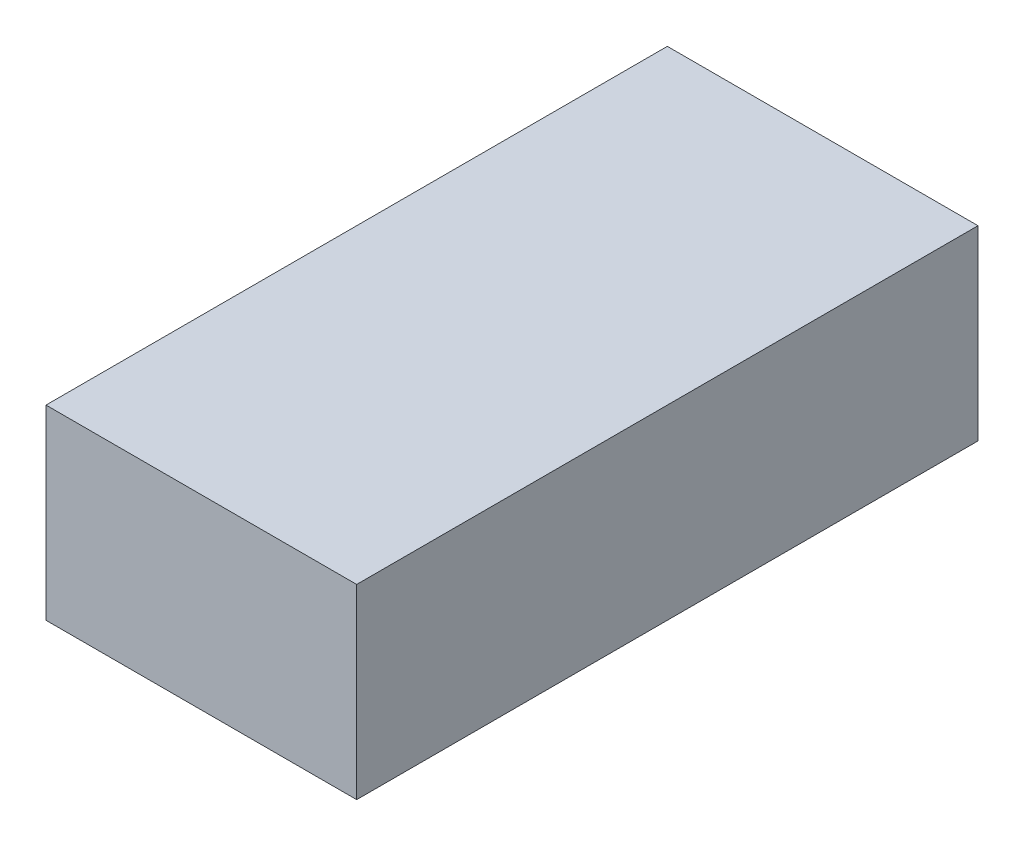
SolidWorks part; units mm, degrees
ref_plane "Front Plane" through (0, 0, 0) normal (0, 0, 1) x (1, 0, 0)
ref_plane "Top Plane" through (0, 0, 0) normal (0, 1, 0) x (1, 0, 0)
ref_plane "Right Plane" through (0, 0, 0) normal (1, 0, 0) x (0, 0, -1)
sketch "Sketch2" plane through (0, 0, 0) normal (1, 0, 0) x (0, 0, -1)
  line L3 (-262.7936, 0) -> (0, 0)
  line L4 (0, 0) -> (203.2, 0)
  line L6 (203.2, 0) -> (203.2, 81.9)
  line L7 (203.2, 81.9) -> (188.2, 81.9)
  line L8 (188.2, 81.9) -> (188.2, 20)
  line L9 (188.2, 20) -> (0, 20)
  line L10 (0, 20) -> (0, 133.7)
  line L11 (0, 133.7) -> (-115, 133.7)
  line L12 (-115, 133.7) -> (-171.1938, 94.3527)
  line L13 (-171.1938, 94.3527) -> (-262.7936, 81.4791)
  line L18 (-262.7936, 81.4791) -> (-262.7936, 31.4791)
  line L19 (-262.7936, 31.4791) -> (-262.7936, 0) construction
  arc A2 (-262.7936, 31.4791) -> (-262.7936, 0) centre (-255.1441, 15.7396) ccw
  dimension "D12" = 17.5
  dimension "D2" = 113.7
  dimension "D3" = 20
  dimension "D4" = 35
  dimension "D5" = 153
  dimension "D6" = 203.2
  dimension "D7" = 15
  dimension "D8" = 61.9
  dimension "D9" = 92.5
  dimension "D10" = 68.6
  dimension "D11" = 50
  dimension "D13" = 115
extrude "Boss-Extrude1" add sketch "Sketch2" along normal mid plane 138
sketch "Sketch4" plane through (0, 20, 0) normal (0, 1, 0) x (1, 0, 0)
  line L0 (69, 188.2) -> (-69, 188.2) construction
  line L1 (69, 0) -> (54, 0)
  line L2 (69, 0) -> (69, 188.2)
  line L3 (69, 188.2) -> (54, 188.2)
  line L4 (54, 0) -> (54, 188.2)
  dimension "D1" = 15
extrude "Boss-Extrude2" add sketch "Sketch4" along normal up to surface (61.9 mm away) up to face at (0, 81.9, -195.7)
mirror "Mirror1" about plane through (0, 0, 0) normal (1, 0, 0) of "Boss-Extrude2"
sketch "Sketch5" plane through (69, 0, 0) normal (1, 0, 0) x (0, 0, -1)
  line L0 (-262.7936, 0) -> (203.2, 0) construction
  line L1 (-224.9441, 0) -> (-160.3441, 0)
  line L2 (28.0559, 0) -> (92.6559, 0)
  arc A0 (-224.9441, 0) -> (-160.3441, 0) centre (-192.6441, 0) ccw
  arc A1 (28.0559, 0) -> (92.6559, 0) centre (60.3559, 0) ccw
  arc A2 (-262.7936, 31.4791) -> (-262.7936, 0) centre (-255.1441, 15.7396) ccw construction
  point P11 (-272.6441, 15.7396)
  dimension "D3" = 32.3
  dimension "D1" = 333
  dimension "D2" = 80
extrude "Boss-Extrude3" add sketch "Sketch5" against normal blind 20.4
mirror "Mirror2" about plane through (0, 0, 0) normal (1, 0, 0) of "Boss-Extrude3"
fillet "Fillet1" radius 10 5 edges at (0, 133.7, 0) (0, 133.7, 115) (0, 94.3527, 171.1938) (0, 81.4791, 262.7936) (0, 31.4791, 262.7936)
sketch "Sketch6" plane through (0, 0, 0) normal (1, 0, 0) x (0, 0, -1)
  line L1 (-2272.5135, -32.3) -> (7727.4865, -32.3)
  line L2 (-2272.5135, -32.3) -> (-2272.5135, 2967.7)
  line L3 (-2272.5135, 2967.7) -> (7727.4865, 2967.7)
  line L4 (7727.4865, -32.3) -> (7727.4865, 2967.7)
  arc A0 (-266.3756, 29.1598) -> (-262.7936, 0) centre (-255.1441, 15.7396) ccw construction
  arc A1 (-224.9441, 0) -> (-160.3441, 0) centre (-192.6441, 0) ccw construction
  point P7 (-272.5135, 13.6059)
  point P11 (-192.6441, -32.3)
  dimension "D1" = 3000
  dimension "D2" = 10000
  dimension "D3" = 2000
extrude "Boss-Extrude4" add sketch "Sketch6" along normal mid plane 5000 separate body
